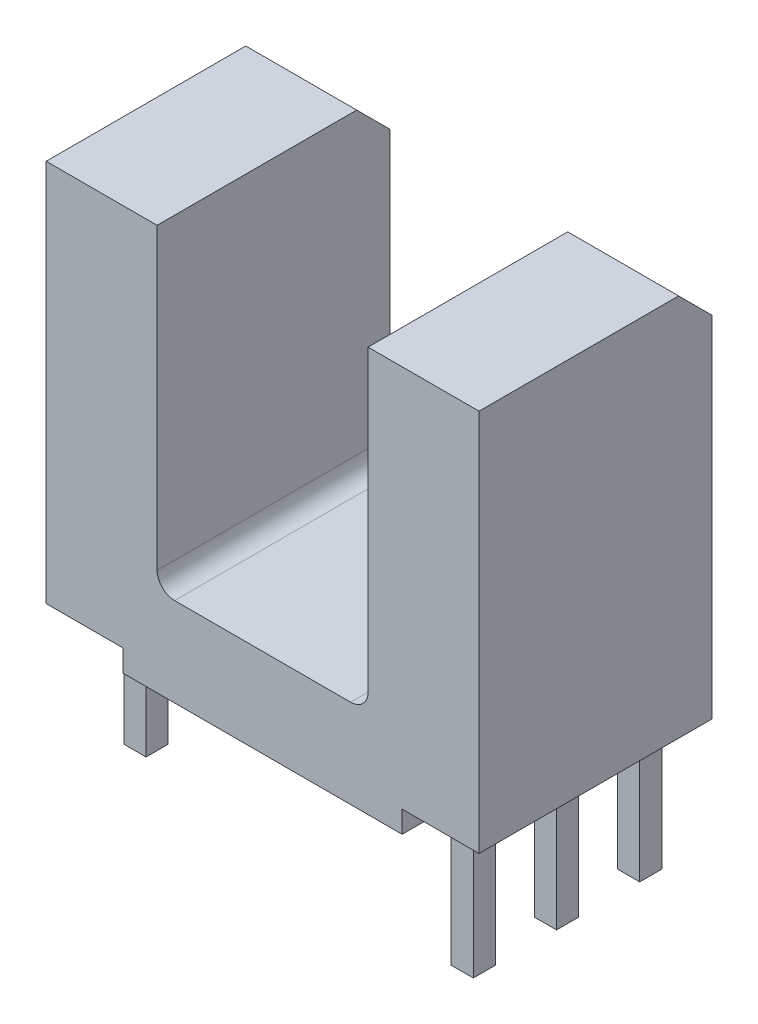
SolidWorks part; units mm, degrees
ref_plane "Front Plane" through (0, 0, 0) normal (0, 0, 1) x (1, 0, 0)
ref_plane "Top Plane" through (0, 0, 0) normal (0, 1, 0) x (1, 0, 0)
ref_plane "Right Plane" through (0, 0, 0) normal (1, 0, 0) x (0, 0, -1)
sketch "Sketch1" plane through (0, 0, 0) normal (0, 0, 1) x (1, 0, 0)
  line L0 (2.415, 9.27) -> (4.955, 9.27)
  line L1 (-4.955, 9.27) -> (-2.415, 9.27)
  line L2 (-4.955, 9.27) -> (-4.955, 0)
  line L3 (-4.955, 0) -> (4.955, 0)
  line L4 (4.955, 9.27) -> (4.955, 0)
  line L5 (2.415, 2.03) -> (-2.415, 2.03)
  line L6 (2.415, 2.03) -> (2.415, 9.27)
  line L8 (-2.415, 2.03) -> (-2.415, 9.27)
  dimension "D1" = 4.83
  dimension "D2" = 2.54
  dimension "D3" = 9.27
  dimension "D4" = 7.24
extrude "Boss-Extrude1" add sketch "Sketch1" along normal mid plane 5.33
chamfer "Chamfer1" distance 0.76 angle 45 3 edges at (3.685, 9.27, -2.665) (-4.955, 4.635, -2.665) (-3.685, 9.27, -2.665)
sketch "Sketch2" plane through (0, 0, 0) normal (0, -1, 0) x (1, 0, 0)
  line L0 (-4.195, -2.665) -> (4.955, -2.665) construction
  line L1 (-3.195, -2.665) -> (-4.955, -2.665)
  line L2 (-3.195, -2.665) -> (-3.195, 2.665)
  line L3 (-3.195, 2.665) -> (-4.955, 2.665)
  line L4 (-4.955, -2.665) -> (-4.955, 2.665)
  line L5 (-4.955, 2.665) -> (4.955, 2.665) construction
  line L6 (4.955, -2.665) -> (3.195, -2.665)
  line L7 (4.955, -2.665) -> (4.955, 2.665)
  line L8 (4.955, 2.665) -> (3.195, 2.665)
  line L9 (3.195, -2.665) -> (3.195, 2.665)
  dimension "D1" = 1.76
extrude "Cut-Extrude1" cut sketch "Sketch2" against normal blind 0.5
fillet "Fillet1" radius 0.4 2 edges at (-2.415, 2.03, 0) (2.415, 2.03, 0)
sketch "Sketch3" plane through (0, 0, 0) normal (0, -1, 0) x (1, 0, 0)
  line L0 (3.81, 0.254) -> (3.81, -0.254)
  line L1 (-4.318, 1.524) -> (-3.81, 1.524)
  line L2 (-4.318, 1.524) -> (-4.318, 1.016)
  line L3 (-4.318, 1.016) -> (-3.81, 1.016)
  line L4 (-3.81, 1.524) -> (-3.81, 1.016)
  line L5 (-4.318, -1.016) -> (-3.81, -1.016)
  line L6 (-4.318, -1.016) -> (-4.318, -1.524)
  line L7 (-4.318, -1.524) -> (-3.81, -1.524)
  line L8 (-3.81, -1.016) -> (-3.81, -1.524)
  line L9 (3.81, 2.159) -> (4.318, 2.159)
  line L10 (3.81, 2.159) -> (3.81, 1.651)
  line L11 (3.81, -2.159) -> (4.318, -2.159)
  line L12 (4.318, 2.159) -> (4.318, 1.651)
  line L13 (4.318, -1.651) -> (3.81, -1.651)
  line L14 (3.81, 0) -> (0, 0) construction
  line L15 (4.318, -0.254) -> (3.81, -0.254)
  line L16 (-3.81, 1.016) -> (-3.81, -1.016) construction
  line L17 (4.318, 0.254) -> (3.81, 0.254)
  line L18 (3.81, -1.651) -> (3.81, -2.159)
  line L19 (4.318, 1.651) -> (3.81, 1.651)
  line L20 (4.318, -1.651) -> (4.318, -2.159)
  line L21 (4.318, 0.254) -> (4.318, -0.254)
  line L22 (0, 0) -> (-3.81, 0) construction
  dimension "D1" = 0.508
  dimension "D2" = 2.54
  dimension "D3" = 8.128
  dimension "D4" = 1.905
  dimension "D5" = 3.81
extrude "Boss-Extrude2" add sketch "Sketch3" along normal blind 2.54 and the other way blind 0.5
